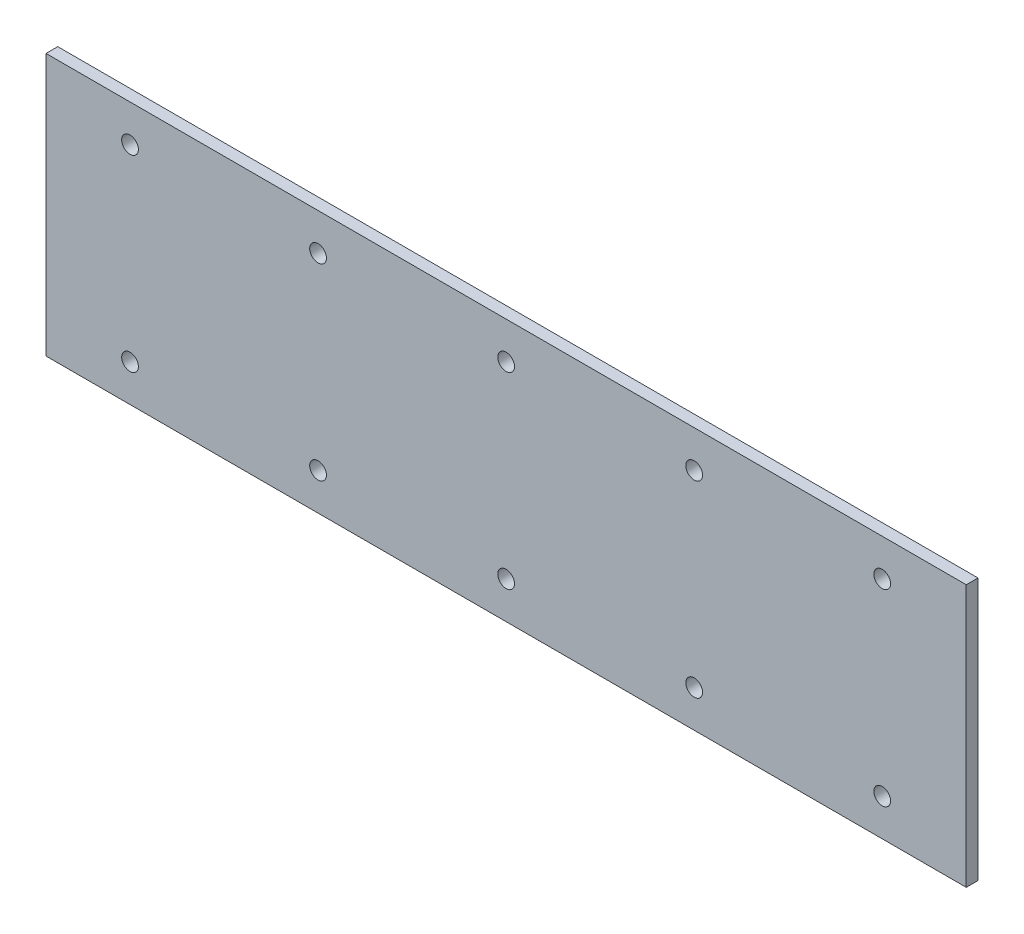
SolidWorks part; units mm, degrees
material "Copper"
ref_plane "Front Plane" through (0, 0, 0) normal (0, 0, 1) x (1, 0, 0)
ref_plane "Top Plane" through (0, 0, 0) normal (0, 1, 0) x (1, 0, 0)
ref_plane "Right Plane" through (0, 0, 0) normal (1, 0, 0) x (0, 0, -1)
sketch "Sketch1" plane through (0, 0, 0) normal (0, 0, 1) x (1, 0, 0)
  line L1 (-62.15, 17.7) -> (62.15, 17.7)
  line L2 (-62.15, 17.7) -> (-62.15, -17.7)
  line L3 (-62.15, -17.7) -> (62.15, -17.7)
  line L4 (62.15, 17.7) -> (62.15, -17.7)
  point P4 (0, 17.7)
  point P6 (-62.15, 0)
  dimension "D1" = 124.3
  dimension "D2" = 35.4
extrude "Boss-Extrude1" add sketch "Sketch1" along normal blind 1.5875
hole_wizard "#4-40 Tapped Hole1" positions "3DSketch1" profile "Sketch2" tap size "#4-40" standard "ANSI Inch" end condition through all
sketch3d "3DSketch1"
  line L3 (-62.15, 17.7, 1.5875) -> (-62.15, -17.7, 1.5875) construction
  line L6 (-62.15, -17.7, 1.5875) -> (62.15, -17.7, 1.5875) construction
  point P0 (-50.8, 12.7, 1.5875)
  point P2 (-50.8, -12.7, 1.5875)
  dimension "D2" = 5
  dimension "D1" = 25.4
  dimension "D3" = 11.35
sketch "Sketch2" plane through (-50.8, 12.7, 1.5875) normal (1, 0, 0) x (0, -1, 0)
  line L0 (0, 0) -> (0, 1.5875)
  line L1 (0, 1.5875) -> (1.1303, 1.5875)
  line L2 (1.1303, 1.5875) -> (1.1303, 0)
  line L5 (1.1303, 0) -> (0, 0)
  line L11 (0, -6.35) -> (0, 107.95) construction
  dimension "Thru Tap Drill Dia." = 2.2606
  dimension "Thru Tap Drill Depth" = 1.5875
cosmetic thread "Hole Thread1" parameters "D2"=2.8448
cosmetic thread "Hole Thread2" parameters "D2"=2.8448
pattern_linear "LPattern1" count 5 spacing 25.4 along (1, 0, 0) of "#4-40 Tapped Hole1"
cosmetic thread "Hole Thread3" parameters "D2"=2.8448
cosmetic thread "Hole Thread4" parameters "D2"=2.8448
cosmetic thread "Hole Thread5" parameters "D2"=2.8448
cosmetic thread "Hole Thread6" parameters "D2"=2.8448
cosmetic thread "Hole Thread7" parameters "D2"=2.8448
cosmetic thread "Hole Thread8" parameters "D2"=2.8448
cosmetic thread "Hole Thread9" parameters "D2"=2.8448
cosmetic thread "Hole Thread10" parameters "D2"=2.8448
equation "\"plate_height\"=35.4"
equation "\"D2@Sketch1\"=\"plate_height\""
equation "\"D2@3DSketch1\"=(\"plate_height\"-\"D1@3DSketch1\")/2"
